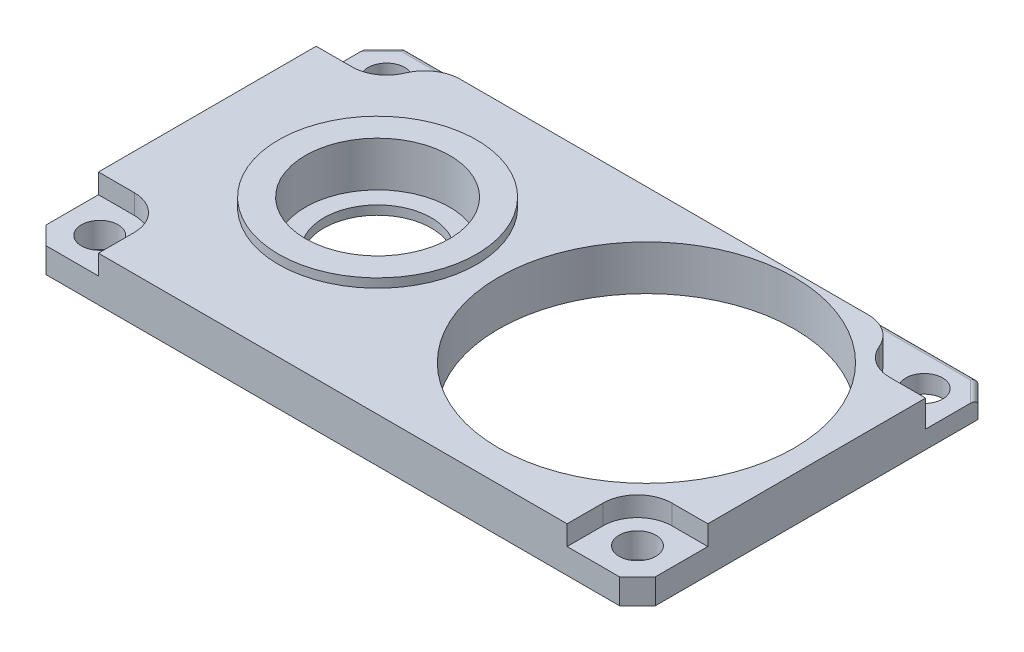
SolidWorks part; units mm, degrees
material "Tough 2000"
ref_plane "Front Plane" through (0, 0, 0) normal (0, 0, 1) x (1, 0, 0)
ref_plane "Top Plane" through (0, 0, 0) normal (0, 1, 0) x (1, 0, 0)
ref_plane "Right Plane" through (0, 0, 0) normal (1, 0, 0) x (0, 0, -1)
sketch "Sketch1" plane through (0, 0, 0) normal (0, 1, 0) x (1, 0, 0)
  line L1 (-17, 10) -> (17, 10)
  line L2 (-17, 10) -> (-17, -10)
  line L3 (-17, -10) -> (17, -10)
  line L4 (17, 10) -> (17, -10)
  line L5 (-17, 10) -> (17, -10) construction
  line L6 (-17, -10) -> (17, 10) construction
  point P0 (0, 0)
  dimension "D1" = 34
  dimension "D2" = 20
extrude "Boss-Extrude1" add sketch "Sketch1" along normal blind 2.5
sketch "Sketch2" plane through (0, 2.5, 0) normal (0, 1, 0) x (1, 0, 0)
  line L0 (-7.5, 0) -> (0, 0) construction
  line L1 (0, 0) -> (7.5, 0) construction
  circle A0 centre (-7.5, 0) radius 3
  circle A1 centre (7.5, 0) radius 8.25
  dimension "D1" = 7.5
  dimension "D2" = 6
  dimension "D3" = 16.5
extrude "Cut-Extrude1" cut sketch "Sketch2" against normal blind 5
sketch "Sketch5" plane through (0, 2.5, 0) normal (0, 1, 0) x (1, 0, 0)
  circle A0 centre (-7.5, 0) radius 4.025
  dimension "D1" = 8.05
extrude "Cut-Extrude4" cut sketch "Sketch5" against normal blind 2
sketch "Sketch3" plane through (0, 2.5, 0) normal (0, 1, 0) x (1, 0, 0)
  line L0 (0, 10) -> (0, 0) construction
  line L1 (17, 10) -> (-17, 10) construction
  line L2 (0, 0) -> (17, 0) construction
  line L3 (17, -10) -> (17, 10) construction
  circle A0 centre (15, 8) radius 1.025
  circle A1 centre (-15, 8) radius 1.025
  circle A2 centre (-15, -8) radius 1.025
  circle A3 centre (15, -8) radius 1.025
  dimension "D1" = 30
  dimension "D2" = 16
  dimension "D3" = 2.05
extrude "Cut-Extrude2" cut sketch "Sketch3" against normal blind 4
sketch "Sketch4" plane through (0, 2.5, 0) normal (0, 1, 0) x (1, 0, 0)
  circle A0 centre (-15, 8) radius 1.925
  circle A1 centre (-15, -8) radius 1.925
  circle A2 centre (15, 8) radius 1.925
  circle A3 centre (15, -8) radius 1.925
  dimension "D1" = 3.85
extrude "Cut-Extrude3" cut sketch "Sketch4" against normal blind 1.5
sketch "Sketch6" plane through (0, 2.5, 0) normal (0, 1, 0) x (1, 0, 0)
  line L14 (0, 0) -> (0, 10) construction
  line L15 (17, 10) -> (-17, 10) construction
  line L16 (17, 10) -> (-17, 10)
  line L17 (-15, 6.075) -> (-17, 6.075)
  line L19 (-17, 10) -> (-17, -10) construction
  line L20 (-17, 6.075) -> (-17, 10)
  line L22 (13.1411, 8.5) -> (-13.1411, 8.5)
  line L23 (17, 6.075) -> (17, 10)
  line L24 (15, 6.075) -> (17, 6.075)
  circle A1 centre (-15, 8) radius 1.925 construction
  arc A3 (-15, 6.075) -> (-13.1411, 8.5) centre (-15, 8) ccw
  arc A5 (15, 6.075) -> (13.1411, 8.5) centre (15, 8) cw
  point P20 (0, 8.5)
  dimension "D1" = 1.5
extrude "Cut-Extrude5" cut sketch "Sketch6" against normal blind 1.5
fillet "Fillet1" radius 2 2 edges at (-13.1411, 1.75, -8.5) (13.1411, 1.75, -8.5)
chamfer "Chamfer1" distance 1 angle 45 4 edges at (17, 1.25, 10) (-17, 1.25, 10) (-17, 0.5, -10) (17, 0.5, -10)
fillet "Fillet2" radius 0.3 3 edges at (-16.5, 1, -9.5) (16.5, 1, -9.5) (0, 1, -10)
sketch "Sketch7" plane through (0, 2.5, 0) normal (0, 1, 0) x (1, 0, 0)
  circle A0 centre (-7.5, 0) radius 4.025
  circle A1 centre (-7.5, 0) radius 5.525
  circle A2 centre (-7.5, 0) radius 4.025 construction
  dimension "D1" = 1.5
extrude "Boss-Extrude2" add sketch "Sketch7" along normal blind 0.5
sketch "Sketch8" plane through (0, 2.5, 0) normal (0, 1, 0) x (1, 0, 0)
  line L0 (-15, -6.075) -> (-17, -6.075)
  line L1 (-17, 6.075) -> (-17, -9) construction
  line L2 (-17, -6.075) -> (-17, -9)
  line L3 (-17, -9) -> (-16, -10)
  line L4 (-16, -10) -> (-13.075, -10)
  line L5 (-16, -10) -> (16, -10) construction
  line L6 (-13.075, -10) -> (-13.075, -8)
  line L7 (0, 0) -> (0, -10) construction
  line L8 (13.075, -10) -> (13.075, -8)
  line L9 (16, -10) -> (13.075, -10)
  line L10 (17, -9) -> (16, -10)
  line L11 (17, -6.075) -> (17, -9)
  line L12 (15, -6.075) -> (17, -6.075)
  circle A0 centre (-15, -8) radius 1.925 construction
  circle A1 centre (-15, -8) radius 1.925 construction
  arc A2 (-15, -6.075) -> (-13.075, -8) centre (-15, -8) ccw
  arc A3 (15, -6.075) -> (13.075, -8) centre (15, -8) cw
extrude "Cut-Extrude6" cut sketch "Sketch8" against normal up to surface (1.5 mm away) up to face at (-15, 1, 9.925)
sketch "Sketch9" plane through (0, 1, 0) normal (0, 1, 0) x (1, 0, 0)
  line L0 (13.075, -8) -> (13.075, -10) construction
  line L1 (13.075, -10) -> (16, -10) construction
  line L2 (16, -10) -> (17, -9) construction
  line L3 (17, -9) -> (17, -6.075) construction
  line L4 (17, -6.075) -> (15, -6.075) construction
  line L5 (-15, -6.075) -> (-17, -6.075) construction
  line L6 (-17, -6.075) -> (-17, -9) construction
  line L7 (-17, -9) -> (-16, -10) construction
  line L8 (-16, -10) -> (-13.075, -10) construction
  line L9 (-13.075, -10) -> (-13.075, -8) construction
  line L10 (13.075, -8) -> (13.075, -10)
  line L11 (13.075, -10) -> (16, -10)
  line L12 (16, -10) -> (17, -9)
  line L13 (17, -9) -> (17, -6.075)
  line L14 (17, -6.075) -> (15, -6.075)
  line L15 (-15, -6.075) -> (-17, -6.075)
  line L16 (-17, -6.075) -> (-17, -9)
  line L17 (-17, -9) -> (-16, -10)
  line L18 (-16, -10) -> (-13.075, -10)
  line L19 (-13.075, -10) -> (-13.075, -8)
  arc A0 (15, -6.075) -> (13.075, -8) centre (15, -8) ccw construction
  arc A1 (-13.075, -8) -> (-15, -6.075) centre (-15, -8) ccw construction
  circle A2 centre (15, -8) radius 1.025 construction
  circle A3 centre (-15, -8) radius 1.025 construction
  arc A4 (15, -6.075) -> (13.075, -8) centre (15, -8) ccw
  arc A5 (-13.075, -8) -> (-15, -6.075) centre (-15, -8) ccw
  circle A6 centre (15, -8) radius 1.025
  circle A7 centre (-15, -8) radius 1.025
extrude "Boss-Extrude3" add sketch "Sketch9" along normal blind 0.4
